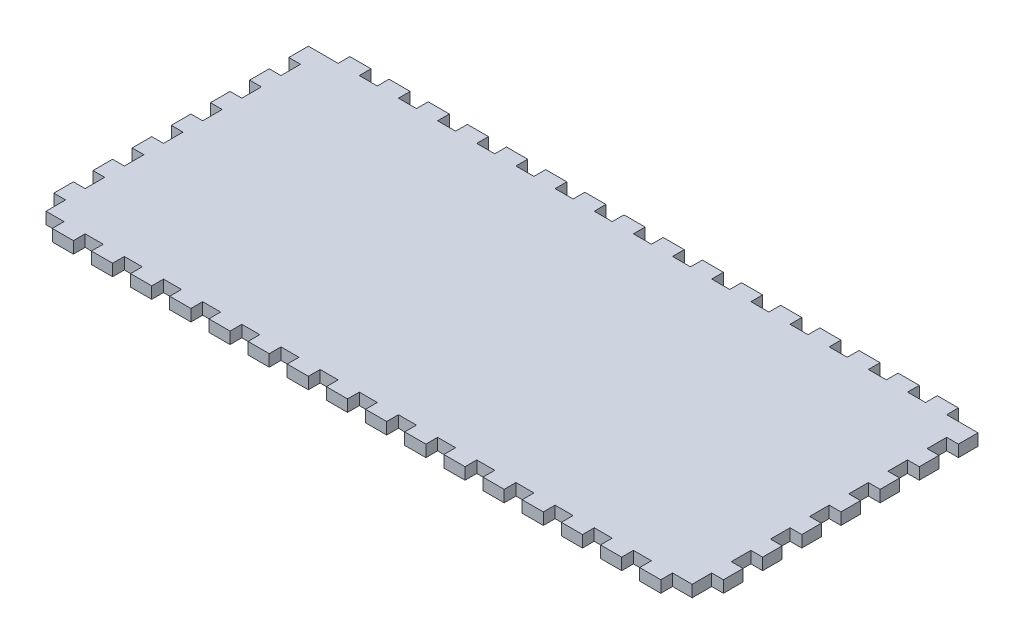
SolidWorks part; units mm, degrees
ref_plane "Спереди" through (0, 0, 0) normal (0, 0, 1) x (1, 0, 0)
ref_plane "Сверху" through (0, 0, 0) normal (0, 1, 0) x (1, 0, 0)
ref_plane "Справа" through (0, 0, 0) normal (1, 0, 0) x (0, 0, -1)
sketch "Эскиз1" plane through (0, 0, 0) normal (0, 1, 0) x (1, 0, 0)
  line L0 (4.6, 70) -> (4.6, 73)
  line L1 (0, 0) -> (4.6, 0)
  line L3 (0, 70) -> (4.6, 70)
  line L5 (4.6, 73) -> (10, 73)
  line L6 (10, 73) -> (10, 70)
  line L7 (82.5, 165) -> (82.5, 0) construction
  line L8 (0, 65) -> (0, 60)
  line L9 (14.6, 70) -> (14.6, 73)
  line L10 (14.6, 73) -> (20, 73)
  line L11 (20, 73) -> (20, 70)
  line L12 (24.6, 70) -> (24.6, 73)
  line L13 (24.6, 73) -> (30, 73)
  line L14 (30, 73) -> (30, 70)
  line L15 (34.6, 70) -> (34.6, 73)
  line L16 (34.6, 73) -> (40, 73)
  line L17 (40, 73) -> (40, 70)
  line L18 (44.6, 70) -> (44.6, 73)
  line L19 (44.6, 73) -> (50, 73)
  line L20 (50, 73) -> (50, 70)
  line L21 (54.6, 70) -> (54.6, 73)
  line L22 (54.6, 73) -> (60, 73)
  line L23 (60, 73) -> (60, 70)
  line L24 (64.6, 70) -> (64.6, 73)
  line L25 (64.6, 73) -> (70, 73)
  line L26 (70, 73) -> (70, 70)
  line L27 (74.6, 70) -> (74.6, 73)
  line L28 (74.6, 73) -> (80, 73)
  line L29 (80, 73) -> (80, 70)
  line L30 (84.6, 70) -> (84.6, 73)
  line L31 (84.6, 73) -> (90, 73)
  line L32 (90, 73) -> (90, 70)
  line L33 (94.6, 70) -> (94.6, 73)
  line L34 (94.6, 73) -> (100, 73)
  line L35 (100, 73) -> (100, 70)
  line L36 (104.6, 70) -> (104.6, 73)
  line L37 (104.6, 73) -> (110, 73)
  line L38 (110, 73) -> (110, 70)
  line L39 (114.6, 70) -> (114.6, 73)
  line L40 (114.6, 73) -> (120, 73)
  line L41 (120, 73) -> (120, 70)
  line L42 (124.6, 70) -> (124.6, 73)
  line L43 (124.6, 73) -> (130, 73)
  line L44 (130, 73) -> (130, 70)
  line L45 (134.6, 70) -> (134.6, 73)
  line L46 (134.6, 73) -> (140, 73)
  line L47 (140, 73) -> (140, 70)
  line L48 (144.6, 70) -> (144.6, 73)
  line L49 (144.6, 73) -> (150, 73)
  line L50 (150, 73) -> (150, 70)
  line L51 (154.6, 70) -> (154.6, 73)
  line L52 (154.6, 73) -> (160, 73)
  line L53 (160, 73) -> (160, 70)
  line L198 (160, 70) -> (168, 70)
  line L199 (150, 70) -> (154.6, 70)
  line L200 (140, 70) -> (144.6, 70)
  line L201 (130, 70) -> (134.6, 70)
  line L202 (120, 70) -> (124.6, 70)
  line L203 (110, 70) -> (114.6, 70)
  line L204 (100, 70) -> (104.6, 70)
  line L205 (90, 70) -> (94.6, 70)
  line L206 (80, 70) -> (84.6, 70)
  line L207 (70, 70) -> (74.6, 70)
  line L208 (60, 70) -> (64.6, 70)
  line L216 (50, 70) -> (54.6, 70)
  line L217 (40, 70) -> (44.6, 70)
  line L218 (30, 70) -> (34.6, 70)
  line L219 (20, 70) -> (24.6, 70)
  line L220 (10, 70) -> (14.6, 70)
  line L269 (165, 65) -> (165, 60)
  line L272 (0, 35) -> (164.6, 35) construction
  line L275 (160, 0) -> (165, 0)
  line L278 (0, 0) -> (4.6, 0)
  line L280 (10, 0) -> (14.6, 0)
  line L284 (20, 0) -> (24.6, 0)
  line L285 (30, 0) -> (34.6, 0)
  line L286 (40, 0) -> (44.6, 0)
  line L287 (50, 0) -> (54.6, 0)
  line L288 (60, 0) -> (64.6, 0)
  line L289 (70, 0) -> (74.6, 0)
  line L290 (80, 0) -> (84.6, 0)
  line L291 (90, 0) -> (94.6, 0)
  line L292 (100, 0) -> (104.6, 0)
  line L293 (110, 0) -> (114.6, 0)
  line L294 (120, 0) -> (124.6, 0)
  line L295 (130, 0) -> (134.6, 0)
  line L296 (140, 0) -> (144.6, 0)
  line L297 (150, 0) -> (154.6, 0)
  line L298 (160, -3) -> (160, 0)
  line L299 (154.6, -3) -> (160, -3)
  line L300 (154.6, 0) -> (154.6, -3)
  line L301 (150, -3) -> (150, 0)
  line L302 (144.6, -3) -> (150, -3)
  line L303 (144.6, 0) -> (144.6, -3)
  line L304 (140, -3) -> (140, 0)
  line L305 (134.6, -3) -> (140, -3)
  line L306 (134.6, 0) -> (134.6, -3)
  line L307 (130, -3) -> (130, 0)
  line L308 (124.6, -3) -> (130, -3)
  line L309 (124.6, 0) -> (124.6, -3)
  line L310 (120, -3) -> (120, 0)
  line L311 (114.6, -3) -> (120, -3)
  line L312 (114.6, 0) -> (114.6, -3)
  line L313 (110, -3) -> (110, 0)
  line L314 (104.6, -3) -> (110, -3)
  line L315 (104.6, 0) -> (104.6, -3)
  line L316 (100, -3) -> (100, 0)
  line L317 (94.6, -3) -> (100, -3)
  line L318 (94.6, 0) -> (94.6, -3)
  line L319 (90, -3) -> (90, 0)
  line L320 (84.6, -3) -> (90, -3)
  line L321 (84.6, 0) -> (84.6, -3)
  line L322 (80, -3) -> (80, 0)
  line L323 (74.6, -3) -> (80, -3)
  line L324 (74.6, 0) -> (74.6, -3)
  line L325 (70, -3) -> (70, 0)
  line L326 (64.6, -3) -> (70, -3)
  line L327 (64.6, 0) -> (64.6, -3)
  line L328 (60, -3) -> (60, 0)
  line L329 (54.6, -3) -> (60, -3)
  line L330 (54.6, 0) -> (54.6, -3)
  line L331 (50, -3) -> (50, 0)
  line L332 (44.6, -3) -> (50, -3)
  line L333 (44.6, 0) -> (44.6, -3)
  line L334 (40, -3) -> (40, 0)
  line L335 (34.6, -3) -> (40, -3)
  line L336 (34.6, 0) -> (34.6, -3)
  line L337 (30, -3) -> (30, 0)
  line L338 (24.6, -3) -> (30, -3)
  line L339 (24.6, 0) -> (24.6, -3)
  line L340 (20, -3) -> (20, 0)
  line L341 (14.6, -3) -> (20, -3)
  line L342 (14.6, 0) -> (14.6, -3)
  line L343 (10, -3) -> (10, 0)
  line L344 (4.6, -3) -> (10, -3)
  line L345 (4.6, 0) -> (4.6, -3)
  line L346 (0, 70) -> (-3, 70)
  line L347 (-3, 70) -> (-3, 65)
  line L348 (-3, 65) -> (0, 65)
  line L349 (-3, 60) -> (-3, 55)
  line L350 (0, 60) -> (-3, 60)
  line L351 (-3, 55) -> (0, 55)
  line L352 (-3, 50) -> (-3, 45)
  line L353 (0, 50) -> (-3, 50)
  line L354 (-3, 45) -> (0, 45)
  line L355 (-3, 40) -> (-3, 35)
  line L356 (0, 40) -> (-3, 40)
  line L357 (-3, 35) -> (0, 35)
  line L358 (-3, 30) -> (-3, 25)
  line L359 (0, 30) -> (-3, 30)
  line L360 (-3, 25) -> (0, 25)
  line L361 (-3, 20) -> (-3, 15)
  line L362 (0, 20) -> (-3, 20)
  line L363 (-3, 15) -> (0, 15)
  line L364 (-3, 10) -> (-3, 5)
  line L365 (0, 10) -> (-3, 10)
  line L366 (-3, 5) -> (0, 5)
  line L367 (168, 5) -> (165, 5)
  line L368 (165, 10) -> (168, 10)
  line L369 (168, 10) -> (168, 5)
  line L370 (168, 15) -> (165, 15)
  line L371 (165, 20) -> (168, 20)
  line L372 (168, 20) -> (168, 15)
  line L373 (168, 25) -> (165, 25)
  line L374 (165, 30) -> (168, 30)
  line L375 (168, 30) -> (168, 25)
  line L376 (168, 35) -> (165, 35)
  line L377 (165, 40) -> (168, 40)
  line L378 (168, 40) -> (168, 35)
  line L379 (168, 45) -> (165, 45)
  line L380 (165, 50) -> (168, 50)
  line L381 (168, 50) -> (168, 45)
  line L382 (168, 55) -> (165, 55)
  line L383 (165, 60) -> (168, 60)
  line L384 (168, 60) -> (168, 55)
  line L385 (168, 65) -> (165, 65)
  line L386 (168, 70) -> (168, 65)
  line L387 (165, 35) -> (165, 30)
  line L388 (0, 55) -> (0, 50)
  line L389 (0, 45) -> (0, 40)
  line L390 (0, 35) -> (0, 30)
  line L391 (0, 25) -> (0, 20)
  line L392 (0, 15) -> (0, 10)
  line L393 (0, 5) -> (0, 0)
  line L394 (165, 55) -> (165, 50)
  line L395 (165, 45) -> (165, 40)
  line L396 (165, 25) -> (165, 20)
  line L397 (165, 15) -> (165, 10)
  line L398 (165, 5) -> (165, 0)
  point P1 (4.6, 0)
  point P12 (7.3, 73)
  point P14 (17.3, 73)
  point P141 (-3, 67.5)
  point P143 (-3, 57.5)
  point P194 (0, 0)
  point P195 (0, 0)
  point P196 (0, 0)
  dimension "D1" = 165
  dimension "D3" = 5.4
  dimension "D4" = 3
  dimension "D5" = 10
  dimension "D6" = 16
  dimension "D7" = 10
  dimension "D8" = 3
  dimension "D9" = 5
  dimension "D10" = 7
  dimension "D11" = 10
extrude "Бобышка-Вытянуть1" add sketch "Эскиз1" along normal blind 3 contours L398 L367 L369 L368 L397 L370 L372 L371 L396 L373 L375 L374 L387 L376 L378 L377 L395 L379 L381 L380 L394 L382 L384 L383 L269 L385 L386 L198 L53 L52 L51 L199 L50 L49 L48 L200 L47 L46 L45 L201 L44 L43 L42 L202 L41 L40 L39 L203 L38 L37 L36
